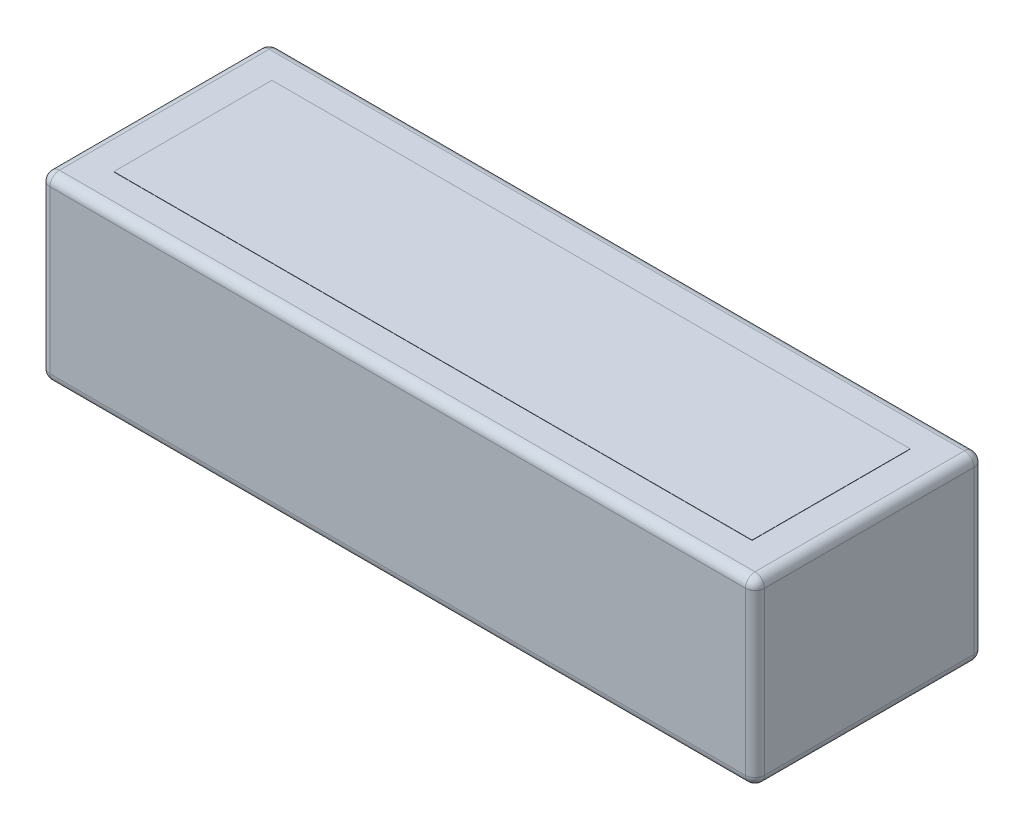
SolidWorks part; units mm, degrees
ref_plane "Front Plane" through (0, 0, 0) normal (0, 0, 1) x (1, 0, 0)
ref_plane "Top Plane" through (0, 0, 0) normal (0, 1, 0) x (1, 0, 0)
ref_plane "Right Plane" through (0, 0, 0) normal (1, 0, 0) x (0, 0, -1)
sketch "Sketch1" plane through (0, 0, 0) normal (0, 1, 0) x (1, 0, 0)
  line L1 (-75, 24) -> (75, 24)
  line L2 (-75, 24) -> (-75, -24)
  line L3 (-75, -24) -> (75, -24)
  line L4 (75, 24) -> (75, -24)
  line L5 (-75, 24) -> (75, -24) construction
  line L6 (-75, -24) -> (75, 24) construction
  point P0 (0, 0)
  dimension "D1" = 150
  dimension "D2" = 48
extrude "Boss-Extrude1" add sketch "Sketch1" along normal blind 38
fillet "Fillet1" radius 2 4 edges at (75, 19, -24) (75, 19, 24) (-75, 19, -24) (-75, 19, 24)
fillet "Fillet2" radius 2 16 edges at (-74.4142, 0, -23.4142) (0, 0, -24) (74.4142, 0, -23.4142) (74.4142, 0, 23.4142) (0, 0, 24) (-74.4142, 0, 23.4142) (-74.4142, 38, -23.4142) (0, 38, -24) (74.4142, 38, -23.4142) (74.4142, 38, 23.4142) (0, 38, 24) (-74.4142, 38, 23.4142) (75, 38, 0) (75, 0, 0) (-75, 0, 0) (-75, 38, 0)
sketch "Sketch3" plane through (0, 38, 0) normal (0, 1, 0) x (1, 0, 0)
  line L1 (-66.9958, 16.5987) -> (66.9958, 16.5987)
  line L2 (-66.9958, 16.5987) -> (-66.9958, -16.5987)
  line L3 (-66.9958, -16.5987) -> (66.9958, -16.5987)
  line L4 (66.9958, 16.5987) -> (66.9958, -16.5987)
  line L5 (-66.9958, 16.5987) -> (66.9958, -16.5987) construction
  line L6 (-66.9958, -16.5987) -> (66.9958, 16.5987) construction
  point P0 (0, 0)
extrude "Boss-Extrude2" add sketch "Sketch3" along normal blind 0.05
